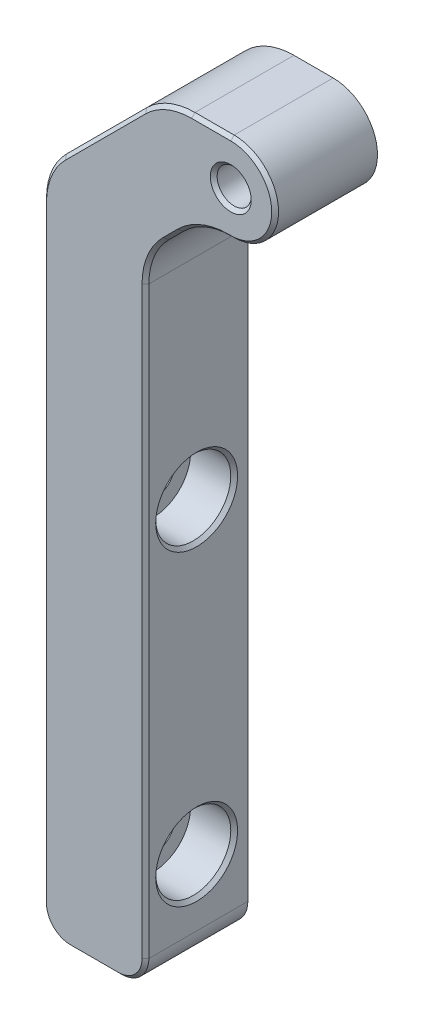
SolidWorks part; units mm, degrees
material "Alumina"
ref_plane "Plan de face" through (0, 0, 0) normal (0, 0, 1) x (1, 0, 0)
ref_plane "Plan de dessus" through (0, 0, 0) normal (0, 1, 0) x (1, 0, 0)
ref_plane "Plan de droite" through (0, 0, 0) normal (1, 0, 0) x (0, 0, -1)
sketch "Sketch1" plane through (0, 0, 0) normal (0, 0, 1) x (1, 0, 0)
  line L0 (2.9141, -75.4592) -> (9.9141, -75.4592)
  line L1 (-1.0859, -71.4592) -> (-1.0859, 17.5334)
  line L2 (13.9141, -71.4592) -> (13.9141, 14.1487)
  line L3 (26.4141, 39.2908) -> (20.6715, 39.2908)
  line L4 (13.6004, 36.3619) -> (1.843, 24.6045)
  line L5 (26.4141, 26.2908) -> (26.0562, 26.2908)
  line L6 (16.843, 21.2197) -> (18.9852, 23.3619)
  arc A1 (26.4141, 26.2908) -> (26.4141, 39.2908) centre (26.4141, 32.7908) ccw
  arc A2 (18.9852, 23.3619) -> (26.0562, 26.2908) centre (26.0562, 16.2908) cw
  arc A3 (16.843, 21.2197) -> (13.9141, 14.1487) centre (23.9141, 14.1487) ccw
  arc A4 (1.843, 24.6045) -> (-1.0859, 17.5334) centre (8.9141, 17.5334) ccw
  arc A5 (20.6715, 39.2908) -> (13.6004, 36.3619) centre (20.6715, 29.2908) ccw
  arc A6 (9.9141, -75.4592) -> (13.9141, -71.4592) centre (9.9141, -71.4592) ccw
  arc A7 (2.9141, -75.4592) -> (-1.0859, -71.4592) centre (2.9141, -71.4592) cw
  point P14 (13.9141, 26.2908)
  dimension "D1" = 6.5
  dimension "D3" = 10
  dimension "D4" = 4
  dimension "D2" = 45
extrude "Boss-Extrude1" add sketch "Sketch1" along normal blind 15
hole_wizard "Tap Drill for M6 Tap1" positions "Sketch2" profile "Sketch3" hole size "M6" standard "ISO" end condition through all
sketch "Sketch2" plane through (0, 0, 15) normal (0, 0, 1) x (1, 0, 0)
  point P0 (26.4141, 32.7908)
sketch "Sketch3" plane through (26.4141, 32.7908, 15) normal (1, 0, 0) x (0, -1, 0)
  line L0 (0, 0) -> (0, 15)
  line L1 (0, 15) -> (2.5, 15)
  line L2 (2.5, 15) -> (2.5, 0)
  line L5 (2.5, 0) -> (0, 0)
  line L11 (0, -6.35) -> (0, 107.95) construction
  dimension "Thru Hole Dia." = 5
  dimension "Thru Hole Depth" = 15
hole_wizard "CBORE for M6 Hex Socket Head Cap Screw1" positions "Sketch4" profile "Sketch5" counterbore size "M6" standard "ISO" end condition through all
sketch "Sketch4" plane through (13.9141, 0, 0) normal (1, 0, 0) x (0, 0, -1)
  line L0 (0, -71.4592) -> (0, 14.1487) construction
  line L1 (-15, 39.2908) -> (0, 39.2908) construction
  point P0 (-7.5, -16.7092)
  point P2 (-7.5, -61.7092)
  point P5 (0, 0)
  dimension "D1" = 45
  dimension "D2" = 7.5
  dimension "D3" = 56
sketch "Sketch5" plane through (13.9141, -16.7092, 7.5) normal (0, 1, 0) x (0, 0, -1)
  line L0 (0, 0) -> (0, 15)
  line L1 (0, 15) -> (3.3, 15)
  line L3 (3.3, 15) -> (3.3, 6.4)
  line L4 (3.3, 6.4) -> (5.5, 6.4)
  line L5 (5.5, 6.4) -> (5.5, 0)
  line L7 (5.5, 0) -> (0, 0)
  line L11 (0, -6.35) -> (0, 107.95) construction
  dimension "Thru Hole Dia." = 6.6
  dimension "Thru Hole Depth" = 15
  dimension "C'Bore Dia." = 11
  dimension "C'Bore Depth" = 6.4
chamfer "Chamfer1" distance 0.5 angle 45 17 edges at (13.9141, -61.7092, 2) (13.9141, -16.7092, 2) (28.9141, 32.7908, 15) (16.8446, 38.5296, 15) (7.7217, 30.4832, 15) (23.5428, 39.2908, 15) (-0.3247, 21.3603, 15) (32.9141, 32.7908, 15) (-1.0859, -26.9629, 15) (26.2352, 26.2908, 15) (0.0857, -74.2876, 15) (22.2294, 25.5296, 15) (6.4141, -75.4592, 15) (17.9141, 22.2908, 15) (12.7425, -74.2876, 15) (14.6753, 17.9755, 15) (13.9141, -28.6553, 15)
